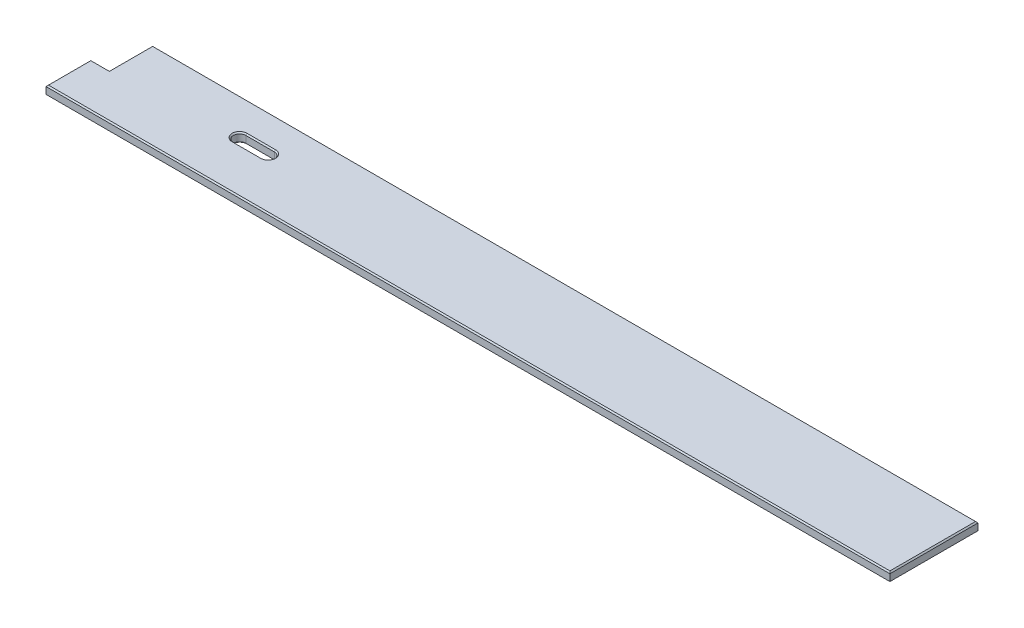
SolidWorks part; units mm, degrees
material "Oak"
ref_plane "Front Plane" through (0, 0, 0) normal (0, 0, 1) x (1, 0, 0)
ref_plane "Top Plane" through (0, 0, 0) normal (0, 1, 0) x (1, 0, 0)
ref_plane "Right Plane" through (0, 0, 0) normal (1, 0, 0) x (0, 0, -1)
sketch "Sketch1" plane through (0, 0, 0) normal (0, 1, 0) x (1, 0, 0)
  line L1 (0, 0) -> (1695.45, 0)
  line L2 (0, 0) -> (0, 180.975)
  line L3 (0, 180.975) -> (1695.45, 180.975)
  line L4 (1695.45, 0) -> (1695.45, 180.975)
  line L6 (254, 118.256) -> (312.7502, 118.256)
  line L8 (254, 92.856) -> (312.7502, 92.856)
  arc A4 (312.7502, 92.856) -> (312.7502, 118.256) centre (312.7502, 105.556) ccw
  arc A5 (254, 118.256) -> (254, 92.856) centre (254, 105.556) ccw
  point P14 (312.7502, 118.256)
  dimension "D7" = 25.4
  dimension "D1" = 180.975
  dimension "D2" = 1695.45
  dimension "D3" = 58.7502
  dimension "D4" = 105.556
  dimension "D5" = 254
extrude "Boss-Extrude1" add sketch "Sketch1" along normal blind 19.05
sketch "Sketch2" plane through (0, 19.05, 0) normal (0, 1, 0) x (1, 0, 0)
  line L0 (0, 180.975) -> (0, 0) construction
  line L1 (0, 0) -> (-38.1, 0)
  line L2 (0, 0) -> (0, 92.075)
  line L3 (0, 92.075) -> (-38.1, 92.075)
  line L4 (-38.1, 0) -> (-38.1, 92.075)
  line L5 (0, 0) -> (1695.45, 0) construction
  dimension "D1" = 38.1
  dimension "D2" = 92.075
extrude "Boss-Extrude3" add sketch "Sketch2" against normal through all
chamfer "Chamfer1" distance 2.54 angle 45 10 edges at (847.725, 19.05, -180.975) (1695.45, 19.05, -90.4875) (828.675, 19.05, 0) (0, 19.05, -136.525) (283.3751, 19.05, -118.256) (283.3751, 19.05, -92.856) (241.3, 19.05, -105.556) (325.4502, 19.05, -105.556) (-38.1, 19.05, -46.0375) (-19.05, 19.05, -92.075)
chamfer "Chamfer2" distance 2.54 angle 45 10 edges at (283.3751, 0, -118.256) (283.3751, 0, -92.856) (828.675, 0, 0) (1695.45, 0, -90.4875) (847.725, 0, -180.975) (0, 0, -136.525) (241.3, 0, -105.556) (325.4502, 0, -105.556) (-19.05, 0, -92.075) (-38.1, 0, -46.0375)
